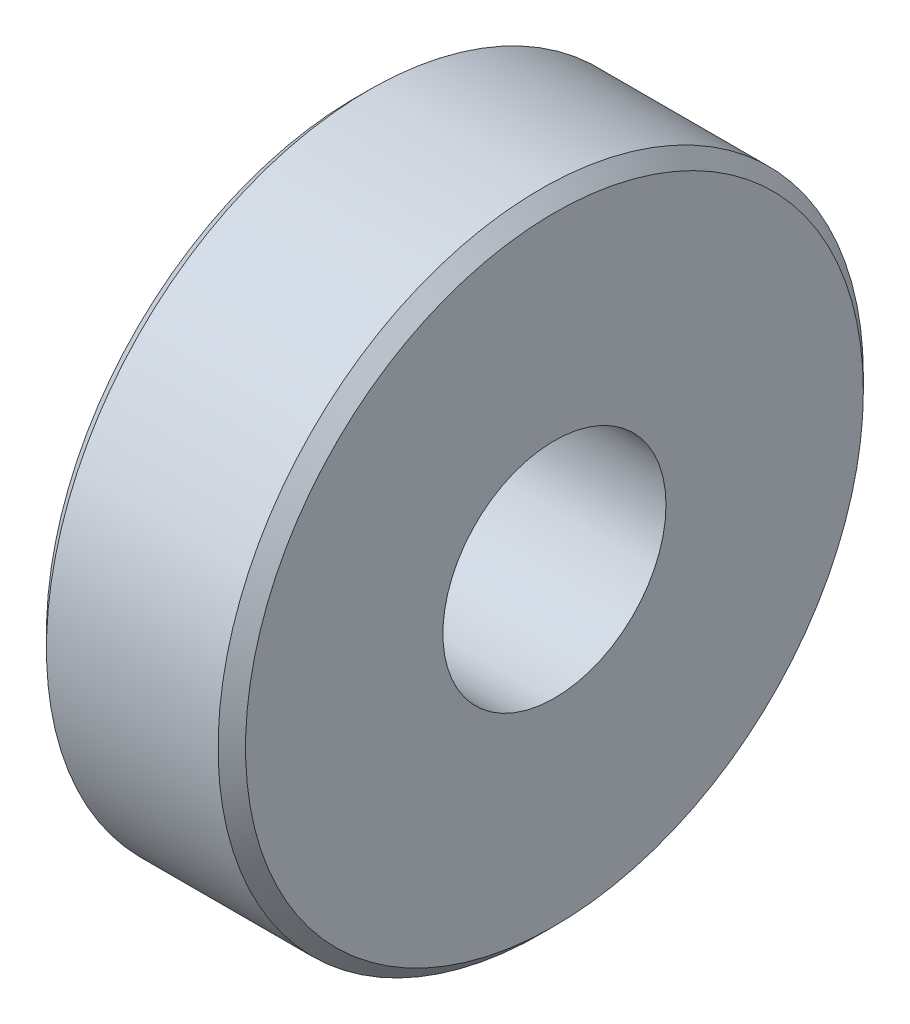
SolidWorks part; units mm, degrees
ref_plane "Front Plane" through (0, 0, 0) normal (0, 0, 1) x (1, 0, 0)
ref_plane "Top Plane" through (0, 0, 0) normal (0, 1, 0) x (1, 0, 0)
ref_plane "Right Plane" through (0, 0, 0) normal (1, 0, 0) x (0, 0, -1)
sketch "Sketch1" plane through (0, 0, 0) normal (0, 0, 1) x (1, 0, 0)
  line L0 (4.1373, 0) -> (-3.9376, 0) construction
  line L1 (1.45, 1.625) -> (1.45, 4.5)
  line L2 (1.25, 4.7) -> (-1.25, 4.7)
  line L3 (-1.45, 4.5) -> (-1.45, 1.625)
  line L4 (-1.45, 1.625) -> (1.45, 1.625)
  line L5 (1.25, 4.7) -> (1.45, 4.5)
  line L6 (0, 1.625) -> (0, 4.7) construction
  line L7 (-1.25, 4.7) -> (-1.45, 4.5)
  dimension "D1" = 2.9
  dimension "D2" = 4.7
  dimension "D3" = 135
  dimension "D4" = 0.2
  dimension "D5" = 3.25
revolve "Revolve1" add sketch "Sketch1" angle 360 about L0
equation "\"D2@Sketch1\" = \"D1@Sketch1\" / 2.5"
